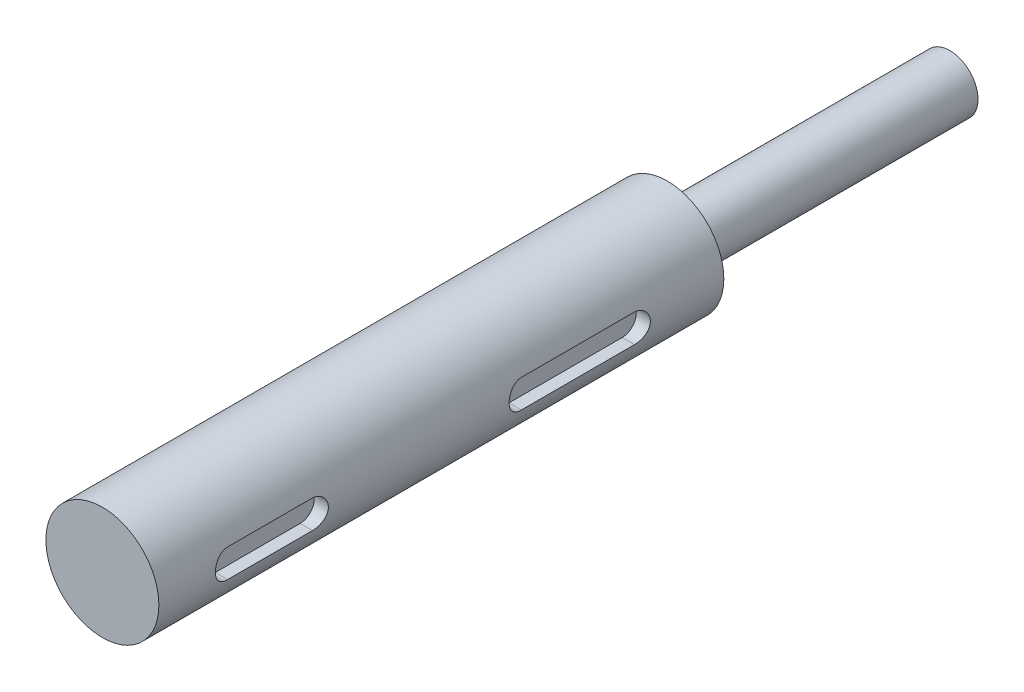
SolidWorks part; units mm, degrees
ref_plane "正面" through (0, 0, 0) normal (0, 0, 1) x (1, 0, 0)
ref_plane "平面" through (0, 0, 0) normal (0, 1, 0) x (1, 0, 0)
ref_plane "右側面" through (0, 0, 0) normal (1, 0, 0) x (0, 0, -1)
sketch "ｽｹｯﾁ1" plane through (0, 0, 0) normal (0, 0, 1) x (1, 0, 0)
  circle A0 centre (0, 0) radius 4
  dimension "D1" = 8
extrude "ﾎﾞｽ - 押し出し1" add sketch "ｽｹｯﾁ1" along normal blind 40
sketch "ｽｹｯﾁ2" plane through (0, 0, 0) normal (0, 0, -1) x (-1, 0, 0)
  circle A0 centre (0, 0) radius 2
  dimension "D1" = 4
extrude "ﾎﾞｽ - 押し出し2" add sketch "ｽｹｯﾁ2" along normal blind 20
ref_plane "平面1" through (3, 0, 0) normal (1, 0, 0) x (0, 0, -1)
sketch "ｽｹｯﾁ3" plane through (3, 0, 0) normal (1, 0, 0) x (0, 0, -1)
  line L0 (0, 0) -> (-40.5336, 0) construction
  line L1 (-35, 0) -> (-29, 0) construction
  line L2 (-35, 1) -> (-29, 1)
  line L3 (-35, -1) -> (-29, -1)
  line L4 (-40, 4) -> (-40, -4) construction
  line L5 (-14.2, 0) -> (-6.2, 0) construction
  line L6 (-14.2, 1) -> (-6.2, 1)
  line L7 (-14.2, -1) -> (-6.2, -1)
  line L8 (0, -4) -> (0, 4) construction
  arc A0 (-35, 1) -> (-35, -1) centre (-35, 0) ccw
  arc A1 (-29, -1) -> (-29, 1) centre (-29, 0) ccw
  arc A2 (-14.2, 1) -> (-14.2, -1) centre (-14.2, 0) ccw
  arc A3 (-6.2, -1) -> (-6.2, 1) centre (-6.2, 0) ccw
  point P5 (-32, 0)
  point P14 (-10.2, 0)
  point P19 (-15.2, 0)
  point P20 (-5.2, 0)
  dimension "D1" = 1
  dimension "D4" = 1
  dimension "D2" = 6
  dimension "D3" = 5
  dimension "D5" = 10
  dimension "D6" = 15.2
extrude "ｶｯﾄ - 押し出し1" cut sketch "ｽｹｯﾁ3" along normal through all
